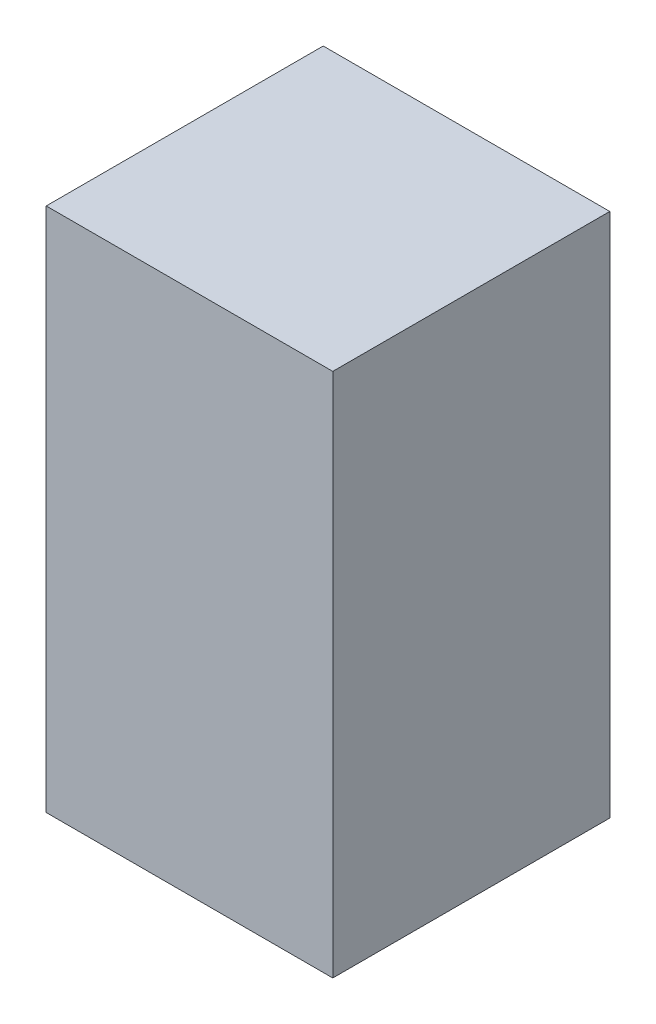
SolidWorks part; units mm, degrees
ref_plane "Front Plane" through (0, 0, 0) normal (0, 0, 1) x (1, 0, 0)
ref_plane "Top Plane" through (0, 0, 0) normal (0, 1, 0) x (1, 0, 0)
ref_plane "Right Plane" through (0, 0, 0) normal (1, 0, 0) x (0, 0, -1)
sketch "Sketch1" plane through (0, 0, 0) normal (0, 1, 0) x (1, 0, 0)
  line L1 (0, 0) -> (1.5, 0)
  line L2 (0, 0) -> (0, 1.45)
  line L3 (0, 1.45) -> (1.5, 1.45)
  line L4 (1.5, 0) -> (1.5, 1.45)
  dimension "D1" = 1.45
  dimension "D2" = 1.5
extrude "Boss-Extrude1" add sketch "Sketch1" along normal blind 2.75
